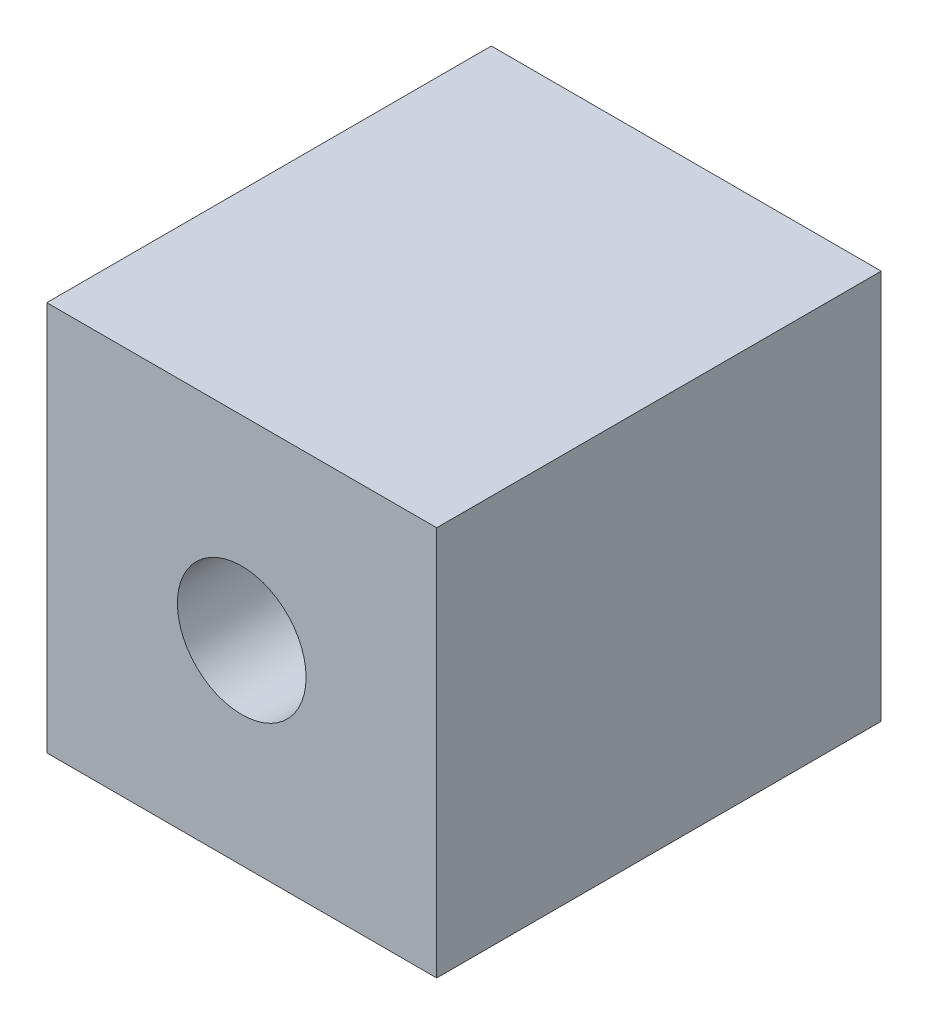
SolidWorks part; units mm, degrees
ref_plane "前视基准面" through (0, 0, 0) normal (0, 0, 1) x (1, 0, 0)
ref_plane "上视基准面" through (0, 0, 0) normal (0, 1, 0) x (1, 0, 0)
ref_plane "右视基准面" through (0, 0, 0) normal (1, 0, 0) x (0, 0, -1)
sketch "草图1" plane through (0, 0, 0) normal (0, 0, 1) x (1, 0, 0)
  line L1 (0, 0) -> (10, 0)
  line L2 (0, 0) -> (0, 10)
  line L3 (0, 10) -> (10, 10)
  line L4 (10, 0) -> (10, 10)
  dimension "D1" = 10
  dimension "D2" = 10
extrude "凸台-拉伸1" add sketch "草图1" along normal blind 11.4
hole_wizard "M4 螺纹孔1" positions "草图2" profile "草图3" tap size "M4" standard "ISO" end condition through all
sketch "草图2" plane through (0, 0, 11.4) normal (0, 0, 1) x (1, 0, 0)
  line L0 (5, 10) -> (5, 0) construction
  line L1 (10, 10) -> (0, 10) construction
  line L2 (0, 0) -> (10, 0) construction
  line L3 (5, 0) -> (5, 5) construction
  line L4 (5, 5) -> (9.0164, 5) construction
  point P0 (5, 5)
  point P13 (0, 0)
cosmetic thread "孔螺蚊线1"
sketch "草图3" plane through (5, 5, 11.4) normal (1, 0, 0) x (0, -1, 0)
  line L0 (0, 0) -> (0, 11.4)
  line L1 (0, 11.4) -> (1.65, 11.4)
  line L2 (1.65, 11.4) -> (1.65, 0)
  line L5 (1.65, 0) -> (0, 0)
  line L11 (0, -6.35) -> (0, 107.95) construction
  dimension "通孔螺纹孔钻头直径" = 3.3
  dimension "通孔螺纹孔钻头深度" = 11.4
